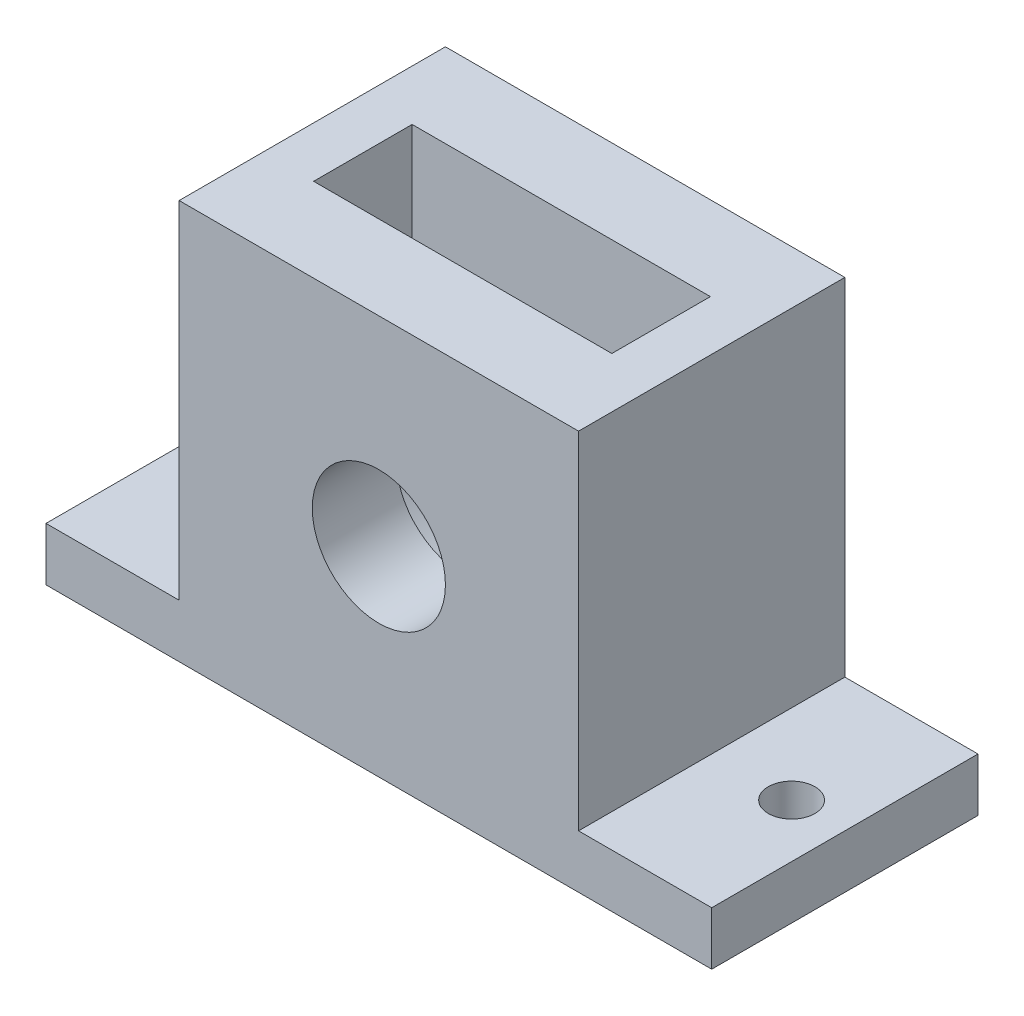
SolidWorks part; units mm, degrees
ref_plane "Front Plane" through (0, 0, 0) normal (0, 0, 1) x (1, 0, 0)
ref_plane "Top Plane" through (0, 0, 0) normal (0, 1, 0) x (1, 0, 0)
ref_plane "Right Plane" through (0, 0, 0) normal (1, 0, 0) x (0, 0, -1)
sketch "Sketch2" plane through (0, 0, 0) normal (0, 0, 1) x (1, 0, 0)
  line L0 (-15, 15) -> (15, -15) construction
  line L1 (-15, -15) -> (15, -15)
  line L2 (-15, -15) -> (-15, 15)
  line L3 (-15, 15) -> (15, 15)
  line L4 (15, -15) -> (15, 15)
  circle A0 centre (0, 0) radius 5
  dimension "D1" = 10
  dimension "D2" = 30
  dimension "D3" = 30
  dimension "D4" = 15
extrude "Boss-Extrude1" add sketch "Sketch2" along normal blind 20
sketch "Sketch3" plane through (0, 0, 0) normal (0, 0, 1) x (1, 0, 0)
  line L0 (-11.2, 15) -> (-11.2, 0)
  line L1 (15, 15) -> (-15, 15) construction
  line L2 (11.2, 15) -> (11.2, 0)
  line L3 (0, 0) -> (0, 15) construction
  line L9 (11.2, 15) -> (-11.2, 15)
  line L11 (-15, -15) -> (15, -15) construction
  arc A2 (-11.2, 0) -> (11.2, 0) centre (0, 0) ccw
  circle A3 centre (0, 0) radius 5 construction
  dimension "D1" = 22.4
  dimension "D2" = 15
ref_plane "Plane1" through (0, 0, 10) normal (0, 0, -1) x (-1, 0, 0)
extrude "Cut-Extrude2" cut sketch "Sketch3" along normal mid plane 7.4 from surface at 10 starting at plane "Plane1"
sketch "Sketch4" plane through (0, -15, 0) normal (0, -1, 0) x (1, 0, 0)
  line L1 (-15, 20) -> (-25, 20)
  line L5 (0, 20) -> (0, 0) construction
  line L6 (-15, 20) -> (-15, 0)
  line L10 (-15, 20) -> (15, 20)
  line L12 (-15, 0) -> (-25, 0)
  line L13 (-25, 20) -> (-25, 0)
  line L14 (15, 20) -> (25, 20)
  line L15 (15, 20) -> (15, 0)
  line L16 (15, 0) -> (25, 0)
  line L17 (25, 20) -> (25, 0)
  circle A3 centre (-21, 10) radius 1.75
  circle A5 centre (21, 10) radius 1.75
  line M6 (15, 0) -> (15, 20)
  line M8 (-15, 20) -> (-15, 0)
  dimension "D10" = 3.5
  dimension "D11" = 3.5
  dimension "D6" = 10
  dimension "D7" = 20
  dimension "D8" = 10
  dimension "D9" = 20
  dimension "D12" = 6
  dimension "D13" = 6
  dimension "D14" = 42
  dimension "D15" = 10
extrude "Boss-Extrude2" add sketch "Sketch4" against normal blind 4 contours L1 L13 L12 A3 M8 | L17 L14 L16 A5 M6
equation "\"centdist\"= \"RD1@Annotations\""
